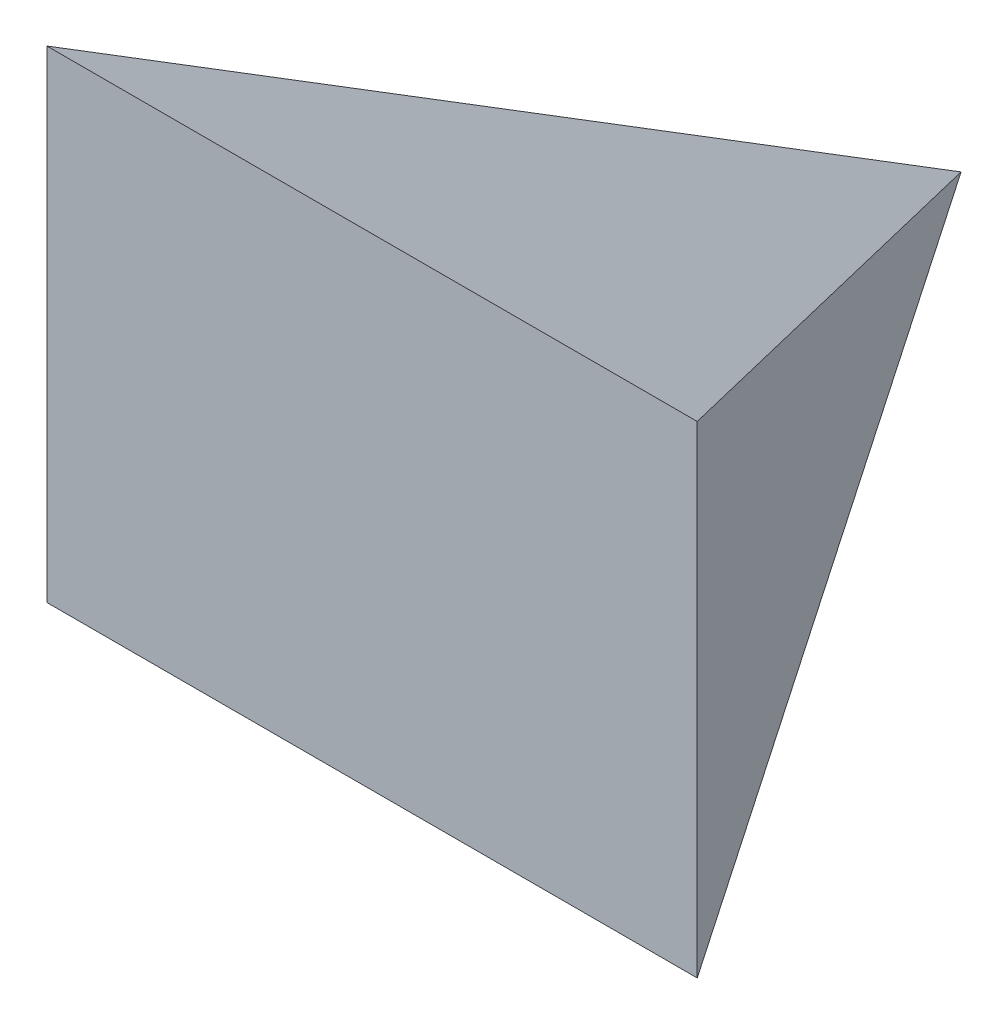
SolidWorks part; units mm, degrees
ref_plane "Front Plane" through (0, 0, 0) normal (0, 0, 1) x (1, 0, 0)
ref_plane "Top Plane" through (0, 0, 0) normal (0, 1, 0) x (1, 0, 0)
ref_plane "Right Plane" through (0, 0, 0) normal (1, 0, 0) x (0, 0, -1)
sketch "Sketch1" plane through (0, 0, 0) normal (0, 1, 0) x (1, 0, 0)
  line L0 (0, 0) -> (-165.6089, -300)
  line L1 (-165.6089, -300) -> (165.6089, -300)
  line L2 (165.6089, -300) -> (0, 0)
  dimension "D1" = 300
  dimension "D2" = 57.8
extrude "Boss-Extrude1" add sketch "Sketch1" along normal blind 250
sketch "Sketch2" plane through (0, 0, 0) normal (1, 0, 0) x (0, 0, -1)
  line L0 (0, 125) -> (-300, 247.7332)
  line L1 (0, 250) -> (0, 0) construction
  line L2 (-300, 250) -> (-300, 0) construction
  line L3 (-300, 247.7332) -> (-300, 2.2668)
  line L4 (-300, 2.2668) -> (0, 125)
  dimension "D1" = 44.5
extrude "Cut-Extrude1" cut sketch "Sketch2" against normal through all and the other way through all flip side to cut
